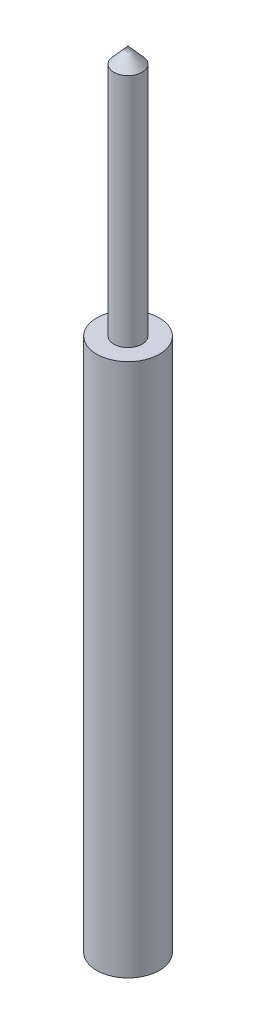
SolidWorks part; units mm, degrees
ref_plane "Plan de face" through (0, 0, 0) normal (0, 0, 1) x (1, 0, 0)
ref_plane "Plan de dessus" through (0, 0, 0) normal (0, 1, 0) x (1, 0, 0)
ref_plane "Plan de droite" through (0, 0, 0) normal (1, 0, 0) x (0, 0, -1)
sketch "Esquisse1" plane through (0, 0, 0) normal (0, 0, 1) x (1, 0, 0)
  line L0 (0, 0) -> (0, 25) construction
  line L1 (0, 25) -> (0.45, 24.5)
  line L2 (0.45, 24.5) -> (0.45, 17)
  line L3 (0.45, 17) -> (1, 17)
  line L4 (1, 17) -> (1, 0)
  line L5 (1, 0) -> (0, 0)
  line L6 (0, 25) -> (0, 0)
  dimension "D1" = 25
  dimension "D2" = 2
  dimension "D3" = 0.9
  dimension "D4" = 0.5
  dimension "D5" = 8
revolve "Révolution1" add sketch "Esquisse1" angle 360 about L0
